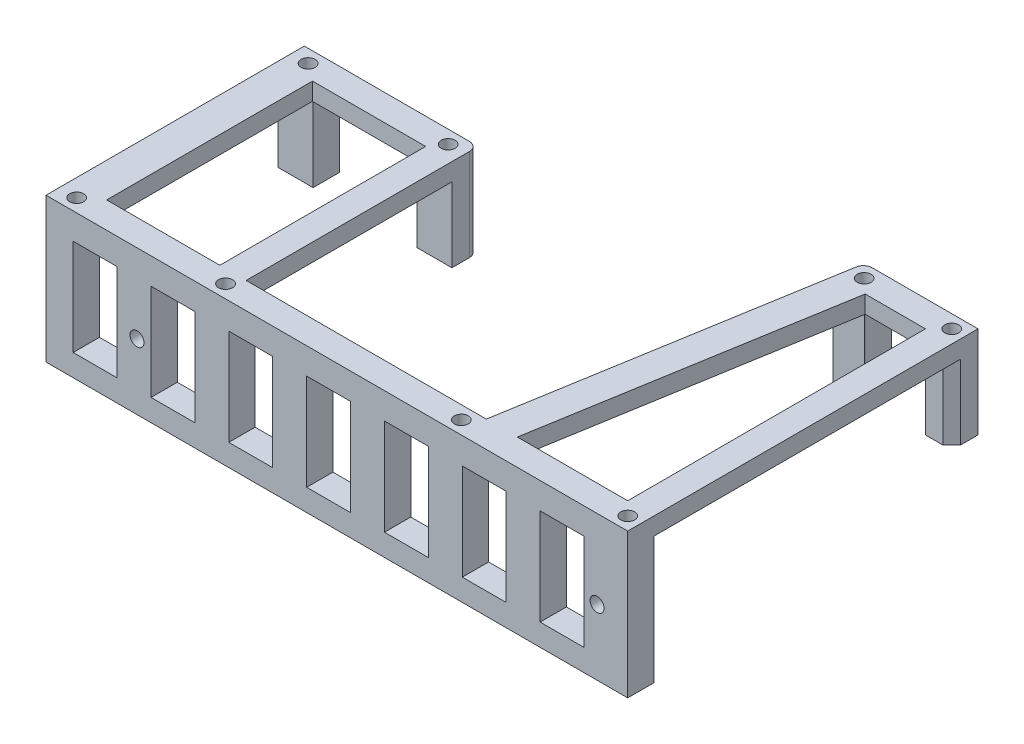
SolidWorks part; units mm, degrees
ref_plane "Спереди" through (0, 0, 0) normal (0, 0, 1) x (1, 0, 0)
ref_plane "Сверху" through (0, 0, 0) normal (0, 1, 0) x (1, 0, 0)
ref_plane "Справа" through (0, 0, 0) normal (1, 0, 0) x (0, 0, -1)
sketch "Эскиз1" plane through (0, 0, 0) normal (0, 1, 0) x (1, 0, 0)
  line L0 (-63, 0) -> (63, 0) construction
  line L1 (63, 0) -> (63, 21) construction
  line L2 (66, 24) -> (66, -56)
  line L3 (66, -56) -> (-66.85, -56)
  line L4 (-66.85, -56) -> (-66.85, 3)
  line L5 (-66.85, 3) -> (-59.15, 3)
  line L6 (-59, -3) -> (-59, -50)
  line L7 (-31, 3) -> (-31, -56) construction
  line L9 (60, 24) -> (66, 24)
  line L10 (-63, 3) -> (-63, -56) construction
  line L11 (63, 24) -> (63, -56) construction
  line L12 (-33.15, -50) -> (-33.15, -3)
  line L13 (-34.85, 3) -> (-27.15, 3)
  line L14 (-27.15, 3) -> (-27.15, -50)
  line L15 (-59, -50) -> (-33.15, -50)
  line L16 (60, 18) -> (60, -50)
  line L17 (-59.15, 3) -> (-34.85, 3)
  line L18 (-59, -3) -> (-33.15, -3)
  line L19 (63, 21) -> (43, 21) construction
  line L20 (60, 24) -> (40.1333, 24)
  line L21 (40.1333, 24) -> (27.7042, -50)
  line L22 (60, 18) -> (46.2236, 18)
  line L23 (46.2236, 18) -> (34.8023, -50)
  line L24 (-27.15, -50) -> (27.7042, -50)
  line L25 (34.8023, -50) -> (60, -50)
  circle A0 centre (63, 21) radius 1.6
  circle A1 centre (-63, 0) radius 1.6
  circle A2 centre (-31, 0) radius 1.6
  circle A3 centre (43, 21) radius 1.6
  point P2 (0, 0)
  point P19 (-31, 0)
  dimension "D9" = 32
  dimension "D10" = 6
  dimension "D12" = 7
  dimension "D2" = 6
  dimension "D3" = 126
  dimension "D4" = 21
  dimension "D5" = 80
  dimension "D6" = 32
  dimension "D7" = 3
  dimension "D8" = 3
  dimension "D11" = 6
  dimension "D13" = 6
  dimension "D14" = 7.85
  dimension "D15" = 6
  dimension "D16" = 3.85
  dimension "D17" = 6
  dimension "D18" = 6
  dimension "D19" = 6
extrude "Бобышка-Вытянуть1" add sketch "Эскиз1" along normal blind 4
sketch "Эскиз2" plane through (0, 0, 0) normal (0, -1, 0) x (1, 0, 0)
  line L0 (-27.15, -3) -> (-66.85, -3) construction
  line L1 (-66.85, 3) -> (-58.85, 3)
  line L2 (-66.85, 3) -> (-66.85, -3)
  line L3 (-66.85, -3) -> (-58.85, -3)
  line L4 (-58.85, 3) -> (-58.85, -3)
  line L5 (-66.85, -3) -> (-66.85, 56) construction
  line L7 (66, -20) -> (66, -24)
  line L8 (60, -18) -> (60, -24)
  line L9 (60, -24) -> (66, -24)
  line L10 (64, -18) -> (60, -18)
  line L11 (60, -18) -> (66, -24) construction
  line L13 (-35.15, 3) -> (-27.15, 3)
  line L14 (-35.15, 3) -> (-35.15, -3)
  line L15 (-35.15, -3) -> (-27.15, -3)
  line L16 (-27.15, 3) -> (-27.15, -3)
  line L19 (46.2236, -18) -> (46.2236, -24)
  line L20 (66, -24) -> (40.1333, -24) construction
  line L21 (46.2236, -24) -> (40.1333, -24)
  line L22 (66, -20) -> (64, -18)
  line L23 (40.1333, -24) -> (27.7042, 50) construction
  line L25 (46.1951, -17.8307) -> (39.0971, -17.8307)
  line L26 (46.2236, -18) -> (34.8023, 50) construction
  line L27 (39.0971, -17.8307) -> (40.1333, -24)
  line L28 (46.1951, -17.8307) -> (46.2236, -18)
  circle A0 centre (63, -21) radius 1.6
  circle A1 centre (-63, 0) radius 1.6
  circle A2 centre (-31, 0) radius 1.6
  circle A3 centre (43, -21) radius 1.6
  point P0 (-63, 0)
  point P7 (63, -21)
  point P18 (-31, 0)
  point P44 (-66.85, 0)
  dimension "D1" = 6
  dimension "D2" = 8
  dimension "D3" = 8
  dimension "D4" = 4
extrude "Бобышка-Вытянуть2" add sketch "Эскиз2" along normal blind 17
fillet "Скругление1" radius 2 2 edges at (-27.15, -6.5, -3) (40.1333, -6.5, -24)
sketch "Эскиз3" plane through (0, 0, 0) normal (0, -1, 0) x (1, 0, 0)
  line L0 (-66.85, 56) -> (66, 56)
  line L1 (66, 56) -> (66, 50)
  line L2 (66, 56) -> (66, -20) construction
  line L3 (66, 50) -> (-66.85, 50)
  line L4 (-66.85, 3) -> (-66.85, 56) construction
  line L5 (-66.85, 50) -> (-66.85, 56)
  line L6 (27.7042, 50) -> (-27.15, 50) construction
  point P4 (-0.425, 50)
extrude "Бобышка-Вытянуть3" add sketch "Эскиз3" along normal blind 29
sketch "Эскиз4" plane through (0, 0, 50) normal (0, 0, -1) x (-1, 0, 0)
  line L1 (15.0953, -24) -> (25.0953, -24)
  line L2 (15.0953, -24) -> (15.0953, -2)
  line L3 (15.0953, -2) -> (25.0953, -2)
  line L4 (25.0953, -24) -> (25.0953, -2)
  line L5 (15.0953, -24) -> (25.0953, -2) construction
  line L6 (15.0953, -2) -> (25.0953, -24) construction
  line L7 (20.0953, -13) -> (2.3215, -13) construction
  line L8 (-2.6785, -24) -> (7.3215, -24)
  line L9 (-2.6785, -24) -> (-2.6785, -2)
  line L10 (-2.6785, -2) -> (7.3215, -2)
  line L11 (7.3215, -24) -> (7.3215, -2)
  line L12 (-2.6785, -24) -> (7.3215, -2) construction
  line L13 (-2.6785, -2) -> (7.3215, -24) construction
  line L14 (-20.4523, -24) -> (-10.4523, -24)
  line L15 (-20.4523, -24) -> (-20.4523, -2)
  line L16 (-20.4523, -2) -> (-10.4523, -2)
  line L17 (-10.4523, -24) -> (-10.4523, -2)
  line L18 (-20.4523, -24) -> (-10.4523, -2) construction
  line L19 (-20.4523, -2) -> (-10.4523, -24) construction
  line L20 (-38.2262, -24) -> (-28.2262, -24)
  line L21 (-38.2262, -24) -> (-38.2262, -2)
  line L22 (-38.2262, -2) -> (-28.2262, -2)
  line L23 (-28.2262, -24) -> (-28.2262, -2)
  line L24 (-38.2262, -24) -> (-28.2262, -2) construction
  line L25 (-38.2262, -2) -> (-28.2262, -24) construction
  line L26 (-56, -24) -> (-46, -24)
  line L27 (-56, -24) -> (-56, -2)
  line L28 (-56, -2) -> (-46, -2)
  line L29 (-46, -24) -> (-46, -2)
  line L30 (-56, -24) -> (-46, -2) construction
  line L31 (-56, -2) -> (-46, -24) construction
  line L32 (2.3215, -13) -> (-15.4523, -13) construction
  line L33 (-15.4523, -13) -> (-33.2262, -13) construction
  line L34 (-33.2262, -13) -> (-51, -13) construction
  line L35 (55.643, -13) -> (37.8692, -13) construction
  line L36 (32.8692, -24) -> (42.8692, -24)
  line L37 (32.8692, -24) -> (32.8692, -2)
  line L38 (32.8692, -2) -> (42.8692, -2)
  line L39 (42.8692, -24) -> (42.8692, -2)
  line L40 (32.8692, -24) -> (42.8692, -2) construction
  line L41 (32.8692, -2) -> (42.8692, -24) construction
  line L42 (50.643, -24) -> (60.643, -24)
  line L43 (50.643, -24) -> (50.643, -2)
  line L44 (50.643, -2) -> (60.643, -2)
  line L45 (60.643, -24) -> (60.643, -2)
  line L46 (50.643, -24) -> (60.643, -2) construction
  line L47 (50.643, -2) -> (60.643, -24) construction
  line L48 (37.8692, -13) -> (20.0953, -13) construction
  line L49 (20.0953, -13) -> (2.3215, -13) construction
  line L50 (66.85, -13) -> (-66, -13) construction
  line L55 (66.85, -29) -> (-66, -29) construction
  point P0 (20.0953, -13)
  point P7 (2.3215, -13)
  point P12 (-15.4523, -13)
  point P17 (-32.648, -11.7281)
  point P22 (-51, -13)
  point P29 (37.8692, -13)
  point P37 (55.643, -13)
  dimension "D1" = 10
  dimension "D2" = 22
  dimension "D3" = 15
  dimension "D4" = 16
extrude "Вырез-Вытянуть1" cut sketch "Эскиз4" against normal through all
sketch "Эскиз5" plane through (0, 4, 0) normal (0, 1, 0) x (1, 0, 0)
  line L0 (-66.85, -53) -> (66, -53) construction
  line L1 (-66.85, 3) -> (-66.85, -56) construction
  line L2 (66, -56) -> (66, 24) construction
  line L3 (-66.85, -56) -> (66, -56) construction
  circle A0 centre (-62.85, -53) radius 1.6
  circle A1 centre (-28.85, -53) radius 1.6
  circle A2 centre (63, -53) radius 1.6
  circle A3 centre (25, -53) radius 1.6
  dimension "D2" = 34
  dimension "D1" = 3
  dimension "D3" = 4
  dimension "D4" = 38
  dimension "D5" = 3
extrude "Вырез-Вытянуть2" cut sketch "Эскиз5" against normal through all
sketch "Эскиз6" plane through (0, 0, 50) normal (0, 0, -1) x (-1, 0, 0)
  line L0 (46.075, 4) -> (46.075, -29) construction
  line L1 (59, 4) -> (33.15, 4) construction
  line L2 (66.85, -29) -> (-66, -29) construction
  line L3 (-59, 4) -> (-59, -29) construction
  line L4 (-34.8023, 4) -> (-60, 4) construction
  line L7 (-66, -29) -> (-66, 0) construction
  circle A0 centre (46.075, -14) radius 1.6
  circle A1 centre (-59, -14) radius 1.6
  dimension "D1" = 15
  dimension "D2" = 15
  dimension "D3" = 7
  dimension "D4" = 105.075
extrude "Вырез-Вытянуть3" cut sketch "Эскиз6" against normal through all
